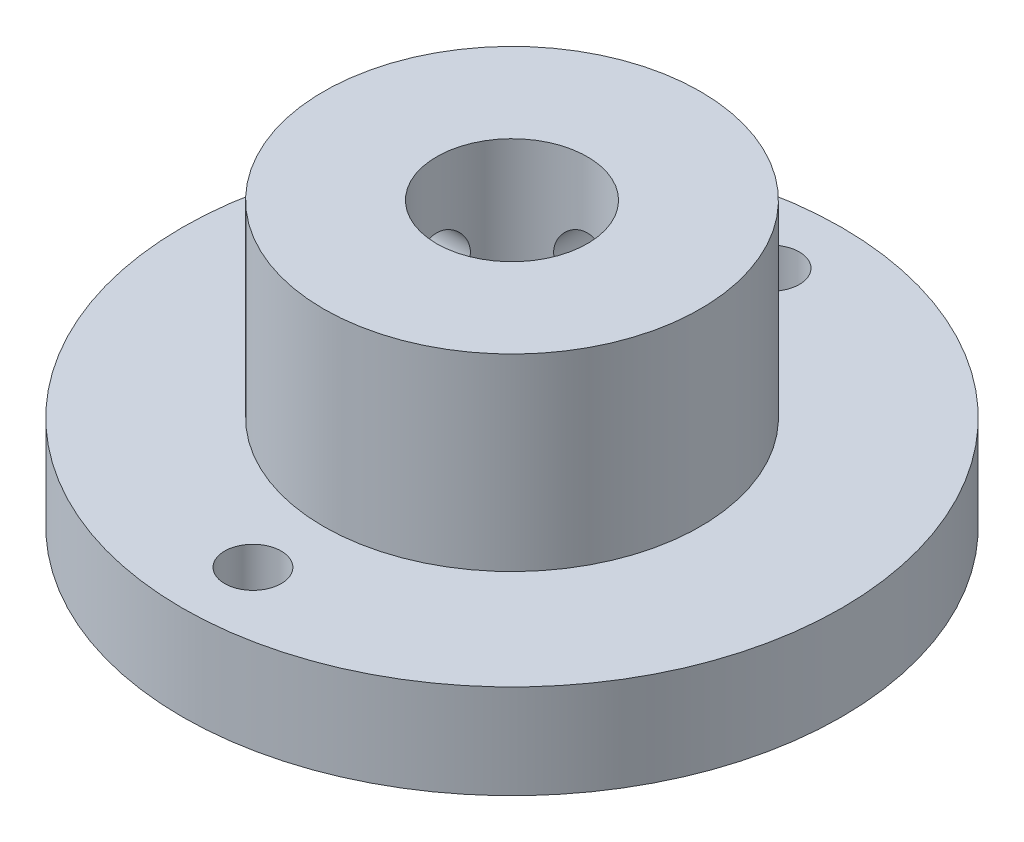
SolidWorks part; units mm, degrees
material "Náilon 101"
ref_plane "Plano frontal" through (0, 0, 0) normal (0, 0, 1) x (1, 0, 0)
ref_plane "Plano superior" through (0, 0, 0) normal (0, 1, 0) x (1, 0, 0)
ref_plane "Plano direito" through (0, 0, 0) normal (1, 0, 0) x (0, 0, -1)
sketch "Esboço1" plane through (0, 0, 0) normal (0, 1, 0) x (1, 0, 0)
  circle A0 centre (0, 0) radius 17.5
  dimension "D1" = 35
extrude "Ressalto-extrusão1" add sketch "Esboço1" along normal blind 5
sketch "Esboço2" plane through (0, 5, 0) normal (0, 1, 0) x (1, 0, 0)
  circle A0 centre (0, 0) radius 10
  dimension "D1" = 20
extrude "Ressalto-extrusão2" add sketch "Esboço2" along normal blind 10
sketch "Esboço3" plane through (0, 15, 0) normal (0, 1, 0) x (1, 0, 0)
  circle A0 centre (0, 0) radius 4
  dimension "D1" = 8
extrude "Corte-extrusão1" cut sketch "Esboço3" against normal through all
sketch "Esboço4" plane through (0, 5, 0) normal (0, 1, 0) x (1, 0, 0)
  line L0 (0, 10) -> (0, 17.5) construction
  circle A0 centre (0, 0) radius 10 construction
  circle A1 centre (0, 0) radius 10 construction
  circle A2 centre (0, 0) radius 17.5 construction
  circle A3 centre (0, 13.75) radius 1.5
  circle A11 centre (0, -13.75) radius 1.5
  point P15 (0, 0.375)
  point P16 (0, 0)
  point P20 (0, 0)
  dimension "D1" = 3
  dimension "D2" = 2
extrude "Corte-extrusão2" cut sketch "Esboço4" against normal blind 10
sketch "Esboço5" plane through (0, 0, 0) normal (0, 0, 1) x (1, 0, 0)
  line L0 (0, 15) -> (0, 5) construction
  line L1 (10, 15) -> (-10, 15) construction
  line L2 (17.5, 5) -> (-17.5, 5) construction
  circle A0 centre (0, 10) radius 1.5
  dimension "D1" = 3
extrude "Corte-extrusão3" cut sketch "Esboço5" against normal through all
sketch "Esboço6" plane through (0, 0, 0) normal (1, 0, 0) x (0, 0, -1)
  line L0 (0, 5) -> (0, 15) construction
  line L1 (17.5, 5) -> (-17.5, 5) construction
  line L2 (10, 15) -> (-10, 15) construction
  circle A0 centre (0, 10) radius 1.5
  dimension "D1" = 3
extrude "Corte-extrusão4" cut sketch "Esboço6" against normal through all
